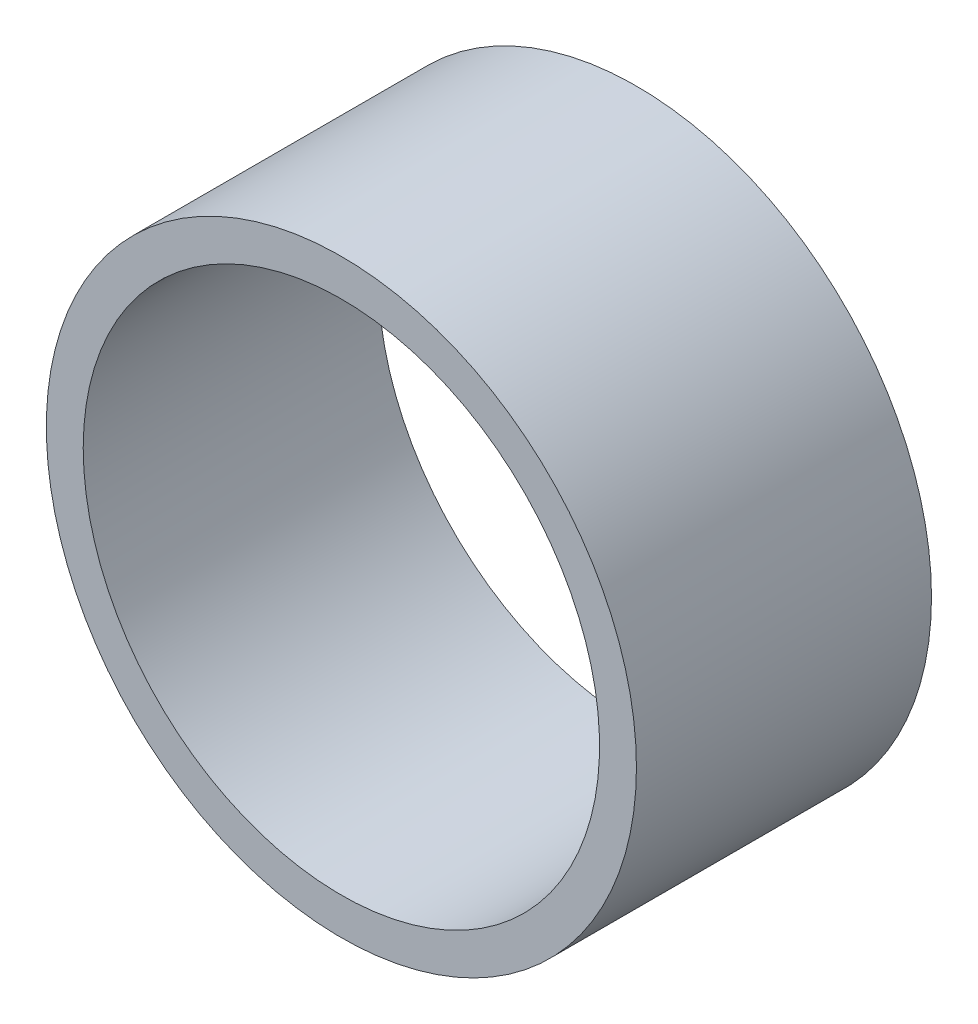
SolidWorks part; units mm, degrees
ref_plane "Спереди" through (0, 0, 0) normal (0, 0, 1) x (1, 0, 0)
ref_plane "Сверху" through (0, 0, 0) normal (0, 1, 0) x (1, 0, 0)
ref_plane "Справа" through (0, 0, 0) normal (1, 0, 0) x (0, 0, -1)
sketch "Эскиз1" plane through (0, 0, 0) normal (0, 0, 1) x (1, 0, 0)
  circle A0 centre (0, 0) radius 16
extrude "Бобышка-Вытянуть1" add sketch "Эскиз1" along normal blind 16
sketch "Эскиз2" plane through (0, 0, 0) normal (0, 0, -1) x (-1, 0, 0)
  circle A0 centre (0, 0) radius 14
extrude "Вырез-Вытянуть1" cut sketch "Эскиз2" against normal through all
